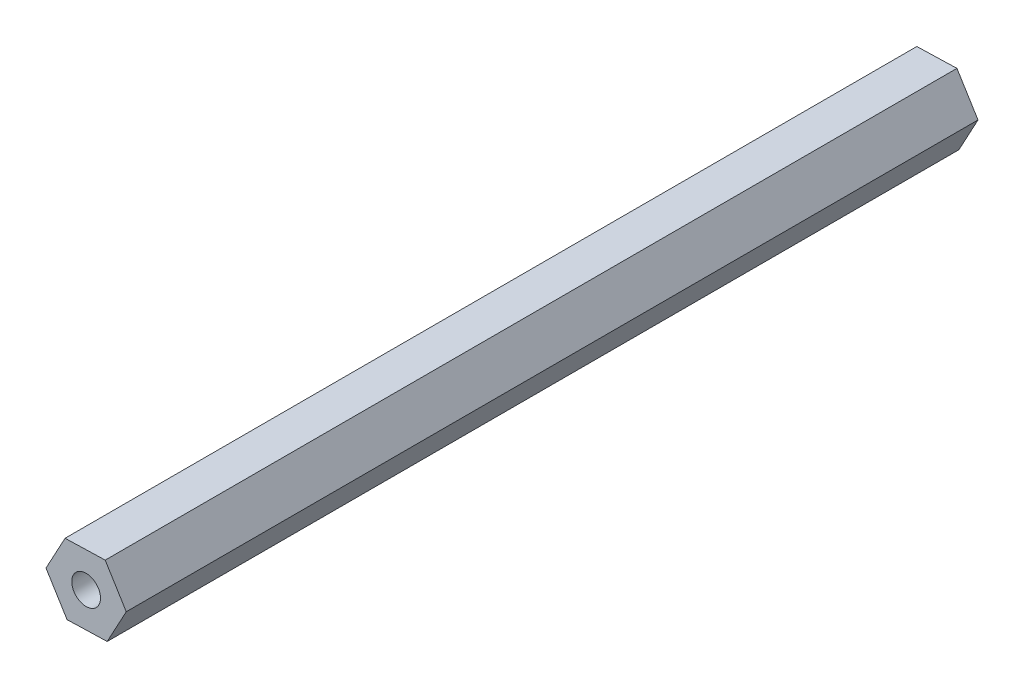
SolidWorks part; units mm, degrees
material "3003 Alloy"
ref_plane "Front Plane" through (0, 0, 0) normal (0, 0, 1) x (1, 0, 0)
ref_plane "Top Plane" through (0, 0, 0) normal (0, 1, 0) x (1, 0, 0)
ref_plane "Right Plane" through (0, 0, 0) normal (1, 0, 0) x (0, 0, -1)
sketch "Sketch1" plane through (0, 0, 0) normal (0, 0, 1) x (1, 0, 0)
  line L1 (3.4845, 6.4515) -> (-3.8449, 6.2434)
  line L2 (-3.8449, 6.2434) -> (-7.3294, -0.2081)
  line L3 (-7.3294, -0.2081) -> (-3.4845, -6.4515)
  line L4 (-3.4845, -6.4515) -> (3.8449, -6.2434)
  line L5 (3.8449, -6.2434) -> (7.3294, 0.2081)
  line L6 (7.3294, 0.2081) -> (3.4845, 6.4515)
  circle A0 centre (0, 0) radius 6.35 construction
  dimension "D1" = 12.7
extrude "Boss-Extrude1" add sketch "Sketch1" along normal blind 155.575
sketch "Sketch3" plane through (0, 0, 155.575) normal (0, 0, 1) x (1, 0, 0)
  circle A0 centre (0, 0) radius 2.6289
  dimension "D1" = 5.2578
extrude "Cut-Extrude2" cut sketch "Sketch3" against normal blind 25.4
sketch "Sketch4" plane through (0, 0, 0) normal (0, 0, -1) x (-1, 0, 0)
  circle A0 centre (0, 0) radius 2.6289
  dimension "D1" = 5.2578
extrude "Cut-Extrude3" cut sketch "Sketch4" against normal blind 25.4
